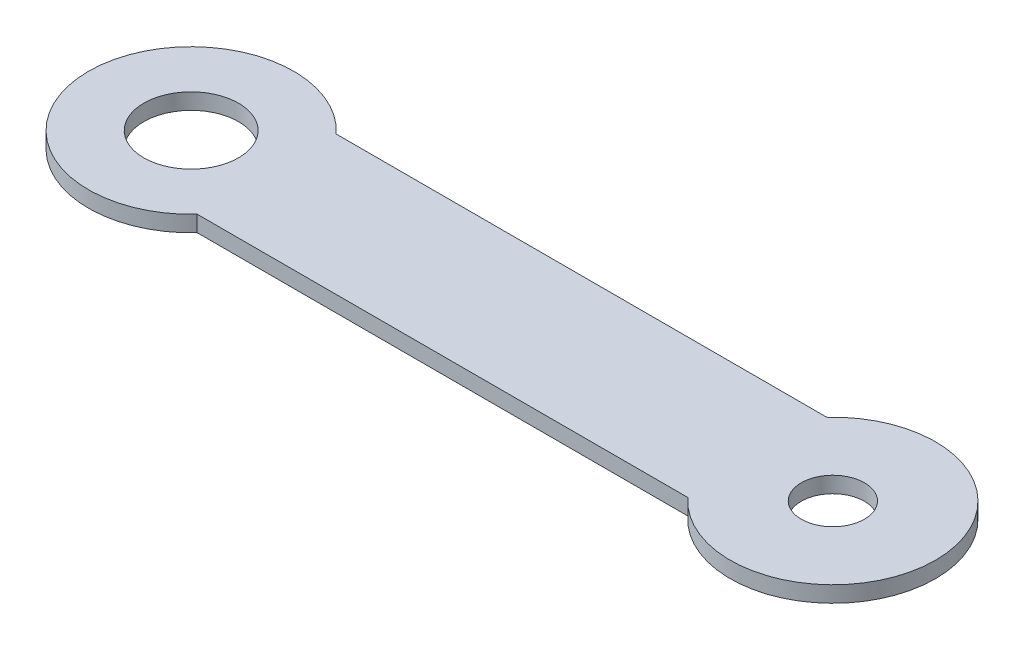
SolidWorks part; units mm, degrees
ref_plane "Front Plane" through (0, 0, 0) normal (0, 0, 1) x (1, 0, 0)
ref_plane "Top Plane" through (0, 0, 0) normal (0, 1, 0) x (1, 0, 0)
ref_plane "Right Plane" through (0, 0, 0) normal (1, 0, 0) x (0, 0, -1)
sketch "Sketch1" plane through (0, 0, 0) normal (0, 1, 0) x (1, 0, 0)
  line L0 (-34.5477, 0) -> (50.8, 0) construction
  line L1 (-38.836, 11) -> (38.836, 11)
  line L2 (-38.836, -11) -> (38.836, -11)
  arc A2 (-38.836, 11) -> (-38.836, -11) centre (-50.8, 0) ccw
  arc A3 (38.836, -11) -> (38.836, 11) centre (50.8, 0) ccw
  point P3 (0, 0)
  dimension "D2" = 16.2523
  dimension "D3" = 32.5046
  dimension "D1" = 22
extrude "Boss-Extrude1" add sketch "Sketch1" along normal blind 2.54
sketch "Sketch2" plane through (0, 2.54, 0) normal (0, 1, 0) x (1, 0, 0)
  circle A0 centre (-50.8, 0) radius 7.5
  circle A1 centre (50.8, 0) radius 5
  dimension "D1" = 15
  dimension "D4" = 10
  dimension "D2" = 50.8
  dimension "D3" = 50.8
extrude "Cut-Extrude1" cut sketch "Sketch2" against normal blind 2.54
